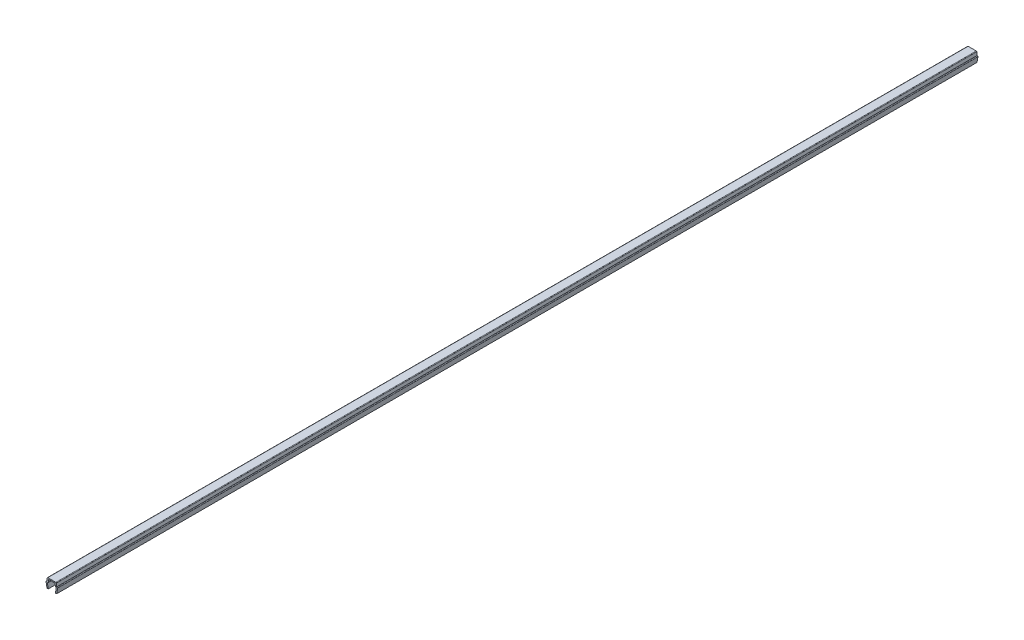
SolidWorks part; units mm, degrees
ref_plane "Front Plane" through (0, 0, 0) normal (0, 0, 1) x (1, 0, 0)
ref_plane "Top Plane" through (0, 0, 0) normal (0, 1, 0) x (1, 0, 0)
ref_plane "Right Plane" through (0, 0, 0) normal (1, 0, 0) x (0, 0, -1)
ref_plane "Plane1" through (0, 0, 0) normal (0, 0, 1) x (1, 0, 0)
sketch "Sketch1" plane through (0, 0, 0) normal (0, 0, 1) x (1, 0, 0)
  line L0 (-3.6, 3.35) -> (-3, 0)
  line L1 (-3, 0) -> (-2.2, 0)
  line L2 (-2.2, 0) -> (-2.7352, 2.9883)
  line L3 (-2.3907, 3.4) -> (-2.2, 3.4)
  line L4 (-2.2, 3.4) -> (-2.0705, 4.8805)
  line L5 (-1.7218, 5.2) -> (1.7218, 5.2)
  line L6 (2.0705, 4.8805) -> (2.2, 3.4)
  line L7 (2.2, 3.4) -> (2.3907, 3.4)
  line L8 (2.7352, 2.9883) -> (2.2, 0)
  line L9 (2.2, 0) -> (3, 0)
  line L10 (3, 0) -> (3.6, 3.35)
  line L11 (3.25, 3.7) -> (3, 3.7)
  line L12 (3, 3.7) -> (2.8355, 5.5805)
  line L13 (2.4868, 5.9) -> (-2.4868, 5.9)
  line L14 (-2.8355, 5.5805) -> (-3, 3.7)
  line L15 (-3, 3.7) -> (-3.25, 3.7)
  arc A0 (-2.7352, 2.9883) -> (-2.3907, 3.4) centre (-2.3907, 3.05) cw
  arc A1 (-2.0705, 4.8805) -> (-1.7218, 5.2) centre (-1.7218, 4.85) cw
  arc A2 (1.7218, 5.2) -> (2.0705, 4.8805) centre (1.7218, 4.85) cw
  arc A3 (2.3907, 3.4) -> (2.7352, 2.9883) centre (2.3907, 3.05) cw
  arc A4 (3.6, 3.35) -> (3.25, 3.7) centre (3.25, 3.35) ccw
  arc A5 (2.8355, 5.5805) -> (2.4868, 5.9) centre (2.4868, 5.55) ccw
  arc A6 (-2.4868, 5.9) -> (-2.8355, 5.5805) centre (-2.4868, 5.55) ccw
  arc A7 (-3.25, 3.7) -> (-3.6, 3.35) centre (-3.25, 3.35) ccw
extrude "Boss-Extrude1" add sketch "Sketch1" against normal mid plane 569.5
sketch "Sketch2" [suppressed] plane through (0, 5.9, 0) normal (0, 1, 0) x (1, 0, 0)
  circle A0 centre (0, 0) radius 2.5
  dimension "D1" = 5
extrude "Cut-Extrude1" [suppressed] cut sketch "Sketch2" against normal blind 1
